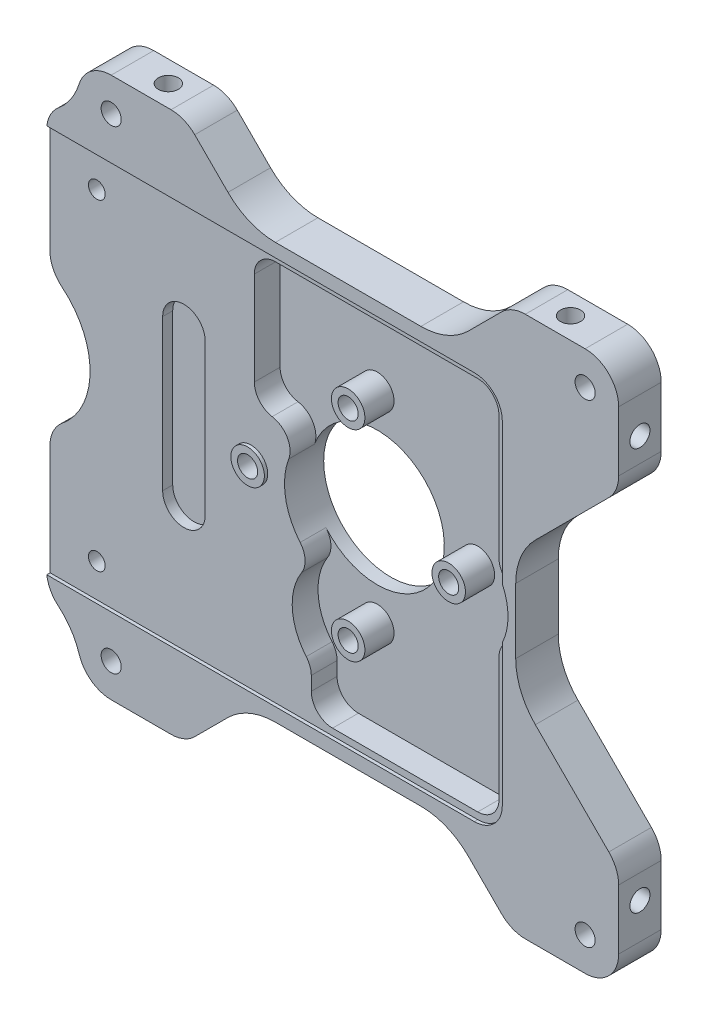
SolidWorks part; units mm, degrees
ref_plane "Front Plane" through (0, 0, 0) normal (0, 0, 1) x (1, 0, 0)
ref_plane "Top Plane" through (0, 0, 0) normal (0, 1, 0) x (1, 0, 0)
ref_plane "Right Plane" through (0, 0, 0) normal (1, 0, 0) x (0, 0, -1)
ref_plane "Plane1" through (0, 0, 6.35) normal (0, 0, 1) x (1, 0, 0)
sketch "Sketch1" plane through (0, 0, 6.35) normal (0, 0, 1) x (1, 0, 0)
  line L0 (15.325, 40.3553) -> (15.325, -40.3553)
  line L1 (15.325, -40.3553) -> (100.6803, -40.3553)
  line L2 (100.6803, -40.3553) -> (100.6803, 40.3553)
  line L3 (100.6803, 40.3553) -> (15.325, 40.3553)
extrude "Boss-Extrude1" add sketch "Sketch1" against normal blind 6.35
sketch "Sketch2" plane through (0, 0, 6.35) normal (0, 0, 1) x (1, 0, 0)
  line L0 (15.325, -28) -> (83.325, -28)
  line L1 (83.325, -28) -> (83.325, -3.7845)
  line L2 (83.325, 3.7845) -> (83.325, 28)
  line L3 (83.325, 28) -> (15.325, 28)
  line L4 (15.325, 28) -> (15.325, -28)
  arc A0 (83.325, -3.7845) -> (83.325, 3.7845) centre (75.325, 0) ccw
extrude "Cut-Extrude1" cut sketch "Sketch2" against normal blind 0.5
sketch "Sketch3" plane through (0, 0, 5.85) normal (0, 0, 1) x (1, 0, 0)
  line L0 (82.325, 5.415) -> (82.325, 28)
  line L1 (82.325, 28) -> (45.825, 28)
  line L2 (45.825, 28) -> (45.825, 10.8749)
  line L3 (54.325, -21.5056) -> (54.325, -28)
  line L4 (54.325, -28) -> (82.325, -28)
  line L5 (82.325, -28) -> (82.325, -5.415)
  arc A0 (45.825, 10.8749) -> (48.4909, 7.7409) centre (49, 10.8749) ccw
  arc A1 (48.4909, 7.7409) -> (50.9563, 3.4968) centre (47.9817, 4.607) cw
  arc A2 (50.9563, 3.4968) -> (54.6339, -8.2226) centre (60.325, 0) cw
  arc A3 (54.6339, -8.2226) -> (54.325, -21.5056) centre (60.325, -15) ccw
  arc A4 (82.325, -5.415) -> (82.325, 5.415) centre (75.325, 0) ccw
extrude "Cut-Extrude2" cut sketch "Sketch3" against normal blind 3.85
sketch "Sketch4" plane through (0, 28, 0) normal (0, -1, 0) x (1, 0, 0)
  line L0 (15.325, 5.85) -> (83.325, 5.85)
  line L1 (83.325, 5.85) -> (83.325, 6.35)
  line L2 (83.325, 6.35) -> (15.325, 6.35)
  line L3 (15.325, 6.35) -> (15.325, 5.85)
extrude "Cut-Extrude3" cut sketch "Sketch4" against normal blind 1
sketch "Sketch5" plane through (0, -28, 0) normal (0, 1, 0) x (-1, 0, 0)
  line L0 (-83.325, 5.85) -> (-15.325, 5.85)
  line L1 (-15.325, 5.85) -> (-15.325, 6.35)
  line L2 (-15.325, 6.35) -> (-83.325, 6.35)
  line L3 (-83.325, 6.35) -> (-83.325, 5.85)
extrude "Cut-Extrude4" cut sketch "Sketch5" against normal blind 1
sketch "Sketch6" plane through (0, 0, 6.35) normal (0, 0, 1) x (1, 0, 0)
  line L0 (20.6438, 40.3553) -> (15.325, 40.3553)
  line L1 (15.325, 40.3553) -> (15.325, 31)
  arc A0 (15.325, 31) -> (20.6438, 40.3553) centre (10.6569, 39.8436) ccw
extrude "Cut-Extrude5" cut sketch "Sketch6" against normal through all
sketch "Sketch7" plane through (0, 0, 6.35) normal (0, 0, 1) x (1, 0, 0)
  line L0 (45.325, 40.3553) -> (45.325, 31)
  line L1 (45.325, 31) -> (75.325, 31)
  line L2 (75.325, 31) -> (75.325, 40.3553)
  line L3 (75.325, 40.3553) -> (45.325, 40.3553)
extrude "Cut-Extrude6" cut sketch "Sketch7" against normal through all
sketch "Sketch8" plane through (0, 0, 6.35) normal (0, 0, 1) x (1, 0, 0)
  line L0 (100.6803, 9) -> (85.325, 9)
  line L1 (85.325, 9) -> (85.325, -9)
  line L2 (85.325, -9) -> (100.6803, -9)
  line L3 (100.6803, -9) -> (100.6803, 9)
extrude "Cut-Extrude7" cut sketch "Sketch8" against normal through all
sketch "Sketch9" plane through (0, 0, 6.35) normal (0, 0, 1) x (1, 0, 0)
  line L0 (15.325, -31) -> (15.325, -40.3553)
  line L1 (15.325, -40.3553) -> (20.6438, -40.3553)
  arc A0 (20.6438, -40.3553) -> (15.325, -31) centre (10.6569, -39.8436) ccw
extrude "Cut-Extrude8" cut sketch "Sketch9" against normal through all
sketch "Sketch10" plane through (0, 0, 6.35) normal (0, 0, 1) x (1, 0, 0)
  line L0 (75.325, -40.3553) -> (75.325, -31)
  line L1 (75.325, -31) -> (45.325, -31)
  line L2 (45.325, -31) -> (45.325, -40.3553)
  line L3 (45.325, -40.3553) -> (75.325, -40.3553)
extrude "Cut-Extrude9" cut sketch "Sketch10" against normal through all
sketch "Sketch11" plane through (0, 0, 5.85) normal (0, 0, 1) x (1, 0, 0)
  line L0 (15.325, 10) -> (15.325, -10)
  arc A0 (15.325, -10) -> (15.325, 10) centre (9.9917, 0) ccw
extrude "Cut-Extrude10" cut sketch "Sketch11" against normal through all
sketch "Sketch12" plane through (0, 0, 5.85) normal (0, 0, 1) x (1, 0, 0)
  line L0 (32.15, 12.5) -> (32.15, -10)
  line L1 (38.5, -10) -> (38.5, 12.5)
  arc A0 (32.15, -10) -> (38.5, -10) centre (35.325, -10) ccw
  arc A1 (38.5, 12.5) -> (32.15, 12.5) centre (35.325, 12.5) ccw
extrude "Cut-Extrude11" cut sketch "Sketch12" against normal blind 1.5
draft "Draft1" type of draft neutral plane draft angle 45 faces to draft 2 face at (45.325, 35.6777, 3.175) face at (75.325, 35.6777, 3.175) neutral plane through (45.325, 31, 0) neutral plane normal (0, 1, 0) parameters "D1"=45
draft "Draft2" type of draft neutral plane draft angle 45 faces to draft 2 face at (45.325, -35.6777, 3.175) face at (75.325, -35.6777, 3.175) neutral plane through (75.325, -31, 0) neutral plane normal (0, -1, 0) parameters "D1"=45
draft "Draft3" type of draft neutral plane draft angle 45 faces to draft 2 face at (93.0027, 9, 3.175) face at (93.0027, -9, 3.175) neutral plane through (85.325, 9, 0) neutral plane normal (1, 0, 0) parameters "D1"=45
ref_plane "Plane2" through (0, 0, 0) normal (0, -1, 0) x (1, 0, 0)
sketch "Sketch13" plane through (0, 0, 0) normal (0, -1, 0) x (1, 0, 0)
  line L0 (70.325, 5.85) -> (60.325, 5.85)
  line L1 (60.325, 5.85) -> (60.325, 0)
  line L2 (60.325, 0) -> (70.325, 0)
  line L3 (70.325, 0) -> (70.325, 5.85)
  line L4 (60.325, 5.85) -> (60.325, 0) construction
revolve "Cut-Revolve1" cut sketch "Sketch13" angle 360 about L4
ref_plane "Plane3" through (0, 15, 0) normal (0, -1, 0) x (1, 0, 0)
sketch "Sketch14" plane through (0, 15, 0) normal (0, -1, 0) x (1, 0, 0)
  line L0 (62.825, 6.35) -> (60.325, 6.35)
  line L1 (60.325, 6.35) -> (60.325, 2)
  line L2 (60.325, 2) -> (62.825, 2)
  line L3 (62.825, 2) -> (62.825, 6.35)
  line L4 (60.325, 6.35) -> (60.325, 2) construction
revolve "Revolve1" add sketch "Sketch14" angle 360 about L4
sketch "Sketch15" plane through (0, 0, 0) normal (0, -1, 0) x (1, 0, 0)
  line L0 (77.825, 6.35) -> (75.325, 6.35)
  line L1 (75.325, 6.35) -> (75.325, 2)
  line L2 (75.325, 2) -> (77.825, 2)
  line L3 (77.825, 2) -> (77.825, 6.35)
  line L4 (75.325, 6.35) -> (75.325, 2) construction
revolve "Revolve2" add sketch "Sketch15" angle 360 about L4
ref_plane "Plane4" through (0, -15, 0) normal (0, -1, 0) x (1, 0, 0)
sketch "Sketch16" plane through (0, -15, 0) normal (0, -1, 0) x (1, 0, 0)
  line L0 (62.825, 6.35) -> (60.325, 6.35)
  line L1 (60.325, 6.35) -> (60.325, 2)
  line L2 (60.325, 2) -> (62.825, 2)
  line L3 (62.825, 2) -> (62.825, 6.35)
  line L4 (60.325, 6.35) -> (60.325, 2) construction
revolve "Revolve3" add sketch "Sketch16" angle 360 about L4
sketch "Sketch17" plane through (0, 0, 0) normal (0, 1, 0) x (1, 0, 0)
  line L0 (47.825, -5.85) -> (45.325, -5.85)
  line L1 (45.325, -5.85) -> (45.325, -6.35)
  line L2 (45.325, -6.35) -> (47.825, -6.35)
  line L3 (47.825, -6.35) -> (47.825, -5.85)
  line L4 (45.325, -5.85) -> (45.325, -6.35) construction
revolve "Revolve4" add sketch "Sketch17" angle 360 about L4
hole_wizard "#2 Clearance Hole1" positions "Sketch19" profile "Sketch18" hole size "#2" standard "ANSI Inch"
sketch "Sketch19" plane through (0, 0, 0) normal (0, 0, -1) x (-1, 0, 0)
  point P0 (-22.325, -24)
  point P1 (-22.325, 24)
sketch "Sketch18" plane through (22.325, -24, 0) normal (1, 0, 0) x (0, 1, 0)
  line L0 (0, 0) -> (0, 6.35)
  line L1 (0, 6.35) -> (1.25, 6.35)
  line L2 (1.25, 6.35) -> (1.25, 0)
  line L5 (1.25, 0) -> (0, 0)
  line L11 (0, -6.35) -> (0, 107.95) construction
  dimension "Thru Hole Dia." = 2.5
  dimension "Thru Hole Depth" = 6.35
hole_wizard "#3 Clearance Hole1" positions "Sketch21" profile "Sketch20" hole size "#3" standard "ANSI Inch"
sketch "Sketch21" plane through (0, 0, 6.35) normal (0, 0, 1) x (1, 0, 0)
  point P0 (45.325, 0)
  point P1 (60.325, 15)
  point P2 (75.325, 0)
  point P3 (60.325, -15)
sketch "Sketch20" plane through (45.325, 0, 6.35) normal (1, 0, 0) x (0, -1, 0)
  line L0 (0, 0) -> (0, 6.35)
  line L1 (0, 6.35) -> (1.5, 6.35)
  line L2 (1.5, 6.35) -> (1.5, 0)
  line L5 (1.5, 0) -> (0, 0)
  line L11 (0, -6.35) -> (0, 107.95) construction
  dimension "Thru Hole Dia." = 3
  dimension "Thru Hole Depth" = 6.35
hole_wizard "#3 Clearance Hole2" positions "Sketch23" profile "Sketch22" hole size "#3" standard "ANSI Inch"
sketch "Sketch23" plane through (0, 0, 0) normal (0, 0, -1) x (-1, 0, 0)
  point P0 (-24.9697, 35.3553)
  point P1 (-95.6803, 35.3553)
  point P2 (-95.6803, -35.3553)
  point P3 (-24.9697, -35.3553)
sketch "Sketch22" plane through (24.9697, 35.3553, 0) normal (1, 0, 0) x (0, 1, 0)
  line L0 (0, 0) -> (0, 6.35)
  line L1 (0, 6.35) -> (1.5, 6.35)
  line L2 (1.5, 6.35) -> (1.5, 0)
  line L5 (1.5, 0) -> (0, 0)
  line L11 (0, -6.35) -> (0, 107.95) construction
  dimension "Thru Hole Dia." = 3
  dimension "Thru Hole Depth" = 6.35
hole_wizard "#3 Clearance Hole3" positions "Sketch25" profile "Sketch24" hole size "#3" standard "ANSI Inch"
sketch "Sketch25" plane through (0, -40.3553, 0) normal (0, -1, 0) x (-1, 0, 0)
  point P0 (-30.325, -3.175)
  point P1 (-90.325, -3.175)
sketch "Sketch24" plane through (30.325, -40.3553, 3.175) normal (1, 0, 0) x (0, 0, -1)
  line L0 (0, 0) -> (0, 12)
  line L1 (0, 12) -> (1.5, 12)
  line L2 (1.5, 12) -> (1.5, 0)
  line L5 (1.5, 0) -> (0, 0)
  line L10 (0, 12) -> (-1.5, 12) construction
  line L11 (0, -6.35) -> (0, 107.95) construction
  dimension "Hole Dia." = 3
  dimension "Hole Depth" = 12
  dimension "Drill Angle" = 180
hole_wizard "#3 Clearance Hole4" positions "Sketch27" profile "Sketch26" hole size "#3" standard "ANSI Inch"
sketch "Sketch27" plane through (0, 40.3553, 0) normal (0, 1, 0) x (1, 0, 0)
  point P0 (90.325, -3.175)
  point P1 (30.325, -3.175)
sketch "Sketch26" plane through (90.325, 40.3553, 3.175) normal (1, 0, 0) x (0, 0, 1)
  line L0 (0, 0) -> (0, 12)
  line L1 (0, 12) -> (1.5, 12)
  line L2 (1.5, 12) -> (1.5, 0)
  line L5 (1.5, 0) -> (0, 0)
  line L10 (0, 12) -> (-1.5, 12) construction
  line L11 (0, -6.35) -> (0, 107.95) construction
  dimension "Hole Dia." = 3
  dimension "Hole Depth" = 12
  dimension "Drill Angle" = 180
hole_wizard "#3 Clearance Hole5" positions "Sketch29" profile "Sketch28" hole size "#3" standard "ANSI Inch"
sketch "Sketch29" plane through (100.6803, 0, 0) normal (1, 0, 0) x (0, 0, -1)
  point P0 (-3.175, -30)
  point P1 (-3.175, 30)
sketch "Sketch28" plane through (100.6803, -30, 3.175) normal (0, 1, 0) x (0, 0, -1)
  line L0 (0, 0) -> (0, 8)
  line L1 (0, 8) -> (1.5, 8)
  line L2 (1.5, 8) -> (1.5, 0)
  line L5 (1.5, 0) -> (0, 0)
  line L10 (0, 8) -> (-1.5, 8) construction
  line L11 (0, -6.35) -> (0, 107.95) construction
  dimension "Hole Dia." = 3
  dimension "Hole Depth" = 8
  dimension "Drill Angle" = 180
fillet "Fillet1" radius 3.175 8 edges at (82.325, 28, 3.925) (82.325, -5.415, 3.925) (54.6339, -8.2226, 3.925) (82.325, 5.415, 3.925) (54.325, -21.5056, 3.925) (54.325, -28, 3.925) (45.825, 28, 3.925) (82.325, -28, 3.925)
fillet "Fillet2" radius 4.175 2 edges at (83.325, -29, 6.1) (83.325, 29, 6.1)
fillet "Fillet3" radius 5 14 edges at (35.9697, -40.3553, 3.175) (84.6803, 40.3553, 3.175) (100.6803, 40.3553, 3.175) (100.6803, -24.3553, 3.175) (15.325, 10, 2.925) (15.325, -10, 2.925) (100.6803, 24.3553, 3.175) (100.6803, -40.3553, 3.175) (35.9697, 40.3553, 3.175) (84.6803, -40.3553, 3.175) (20.6438, 40.3553, 3.175) (15.325, 31, 3.175) (15.325, -31, 3.175) (20.6438, -40.3553, 3.175)
fillet "Fillet4" radius 10 6 edges at (75.325, 31, 3.175) (75.325, -31, 3.175) (45.325, 31, 3.175) (85.325, -9, 3.175) (85.325, 9, 3.175) (45.325, -31, 3.175)
